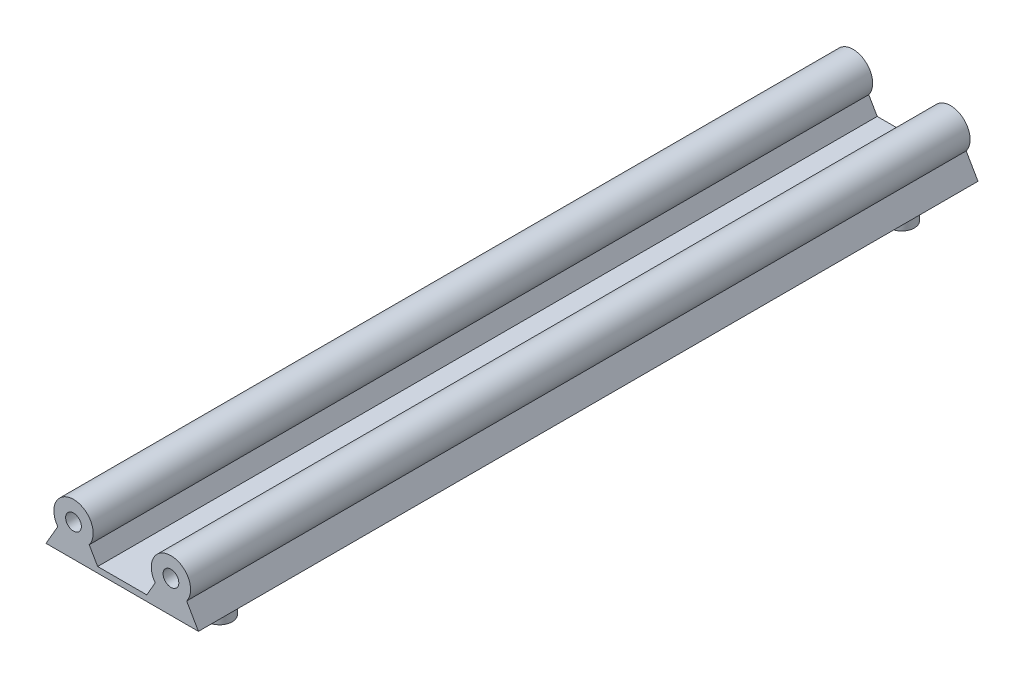
SolidWorks part; units mm, degrees
ref_plane "Front Plane" through (0, 0, 0) normal (0, 0, 1) x (1, 0, 0)
ref_plane "Top Plane" through (0, 0, 0) normal (0, 1, 0) x (1, 0, 0)
ref_plane "Right Plane" through (0, 0, 0) normal (1, 0, 0) x (0, 0, -1)
sketch "Sketch1" plane through (0, 0, 0) normal (0, 0, 1) x (1, 0, 0)
  line L0 (-4, -3) -> (4, -3) construction
  line L1 (-4, -3) -> (-7, -8.1962)
  line L2 (4, -3) -> (7, -8.1962)
  line L3 (-7, -8.1962) -> (7, -8.1962)
  line L4 (28.8, -3) -> (31.8, -8.1962)
  line L5 (17.8, -8.1962) -> (31.8, -8.1962)
  line L6 (20.8, -3) -> (17.8, -8.1962)
  circle A0 centre (0, 0) radius 5
  arc A1 (-4, -3) -> (4, -3) centre (0, 0) cw
  arc A2 (20.8, -3) -> (28.8, -3) centre (24.8, 0) cw
  dimension "D1" = 3
  dimension "D2" = 2
  dimension "D3" = 8
extrude "Boss-Extrude1" add sketch "Sketch1" along normal blind 220 contours A0 L0 | L0 A0 | A0 L1 L3 L2 | L4 L5 L6 A2
sketch "Sketch3" plane through (0, 0, 220) normal (0, 0, 1) x (1, 0, 0)
  line L0 (7, -8.1962) -> (17.8, -8.1962)
  line L1 (6.15, -6.7239) -> (18.65, -6.7239)
  line L2 (4, -3) -> (7, -8.1962) construction
  line L3 (20.8, -3) -> (17.8, -8.1962) construction
  line L4 (18.65, -6.7239) -> (18.65, -8.1962)
  line L5 (17.8, -8.1962) -> (31.8, -8.1962) construction
  line L6 (18.65, -8.1962) -> (17.8, -8.1962)
  line L7 (6.15, -6.7239) -> (6.15, -8.1962)
  line L8 (-7, -8.1962) -> (7, -8.1962) construction
  line L9 (6.15, -8.1962) -> (7, -8.1962)
  dimension "D1" = 12.5
sketch "Sketch4" plane through (0, -8.1962, 0) normal (0, -1, 0) x (1, 0, 0)
  line L0 (24.8, 220) -> (24.8, 0) construction
  line L1 (17.8, 220) -> (31.8, 220) construction
  line L2 (17.8, 0) -> (31.8, 0) construction
  line L3 (0, 0) -> (0, 220) construction
  line L4 (-7, 220) -> (7, 220) construction
  circle A0 centre (0, 196.8) radius 3.2
  circle A1 centre (24.8, 196.8) radius 3.2
  circle A2 centre (24.8, 172) radius 3.2
  circle A3 centre (24.8, 147.2) radius 3.2
  circle A4 centre (24.8, 122.4) radius 3.2
  circle A5 centre (24.8, 97.6) radius 3.2
  circle A6 centre (24.8, 72.8) radius 3.2
  circle A7 centre (24.8, 48) radius 3.2
  circle A8 centre (24.8, 23.2) radius 3.2
  circle A9 centre (0, 172) radius 3.2
  circle A10 centre (0, 147.2) radius 3.2
  circle A11 centre (0, 122.4) radius 3.2
  circle A12 centre (0, 97.6) radius 3.2
  circle A13 centre (0, 72.8) radius 3.2
  circle A14 centre (0, 48) radius 3.2
  circle A15 centre (0, 23.2) radius 3.2
  dimension "D1" = 2
  dimension "D3" = 23.2
  dimension "D2" = 8
extrude "Boss-Extrude3" add sketch "Sketch4" along normal blind 6
extrude "Boss-Extrude4" add sketch "Sketch3" against normal blind 220
sketch "Sketch5" plane through (0, 0, 0) normal (0, 0, -1) x (-1, 0, 0)
  circle A0 centre (0, 0) radius 1.37
  circle A1 centre (-24.8, 0) radius 1.37
  dimension "D1" = 2
extrude "Cut-Extrude1" cut sketch "Sketch5" against normal blind 7
sketch "Sketch6" plane through (0, 0, 220) normal (0, 0, 1) x (1, 0, 0)
  circle A0 centre (0, 0) radius 1.37
  circle A1 centre (24.8, 0) radius 1.37
  dimension "D1" = 2
extrude "Cut-Extrude2" cut sketch "Sketch6" against normal blind 7
sketch "Sketch7" plane through (0, -14.1962, 0) normal (0, -1, 0) x (1, 0, 0)
  circle A0 centre (0, 172) radius 3.2
  circle A1 centre (24.8, 172) radius 3.2
  circle A2 centre (24.8, 147.2) radius 3.2
  circle A3 centre (24.8, 122.4) radius 3.2
  circle A4 centre (24.8, 97.6) radius 3.2
  circle A5 centre (24.8, 72.8) radius 3.2
  circle A6 centre (24.8, 48) radius 3.2
  circle A7 centre (0, 147.2) radius 3.2
  circle A8 centre (0, 122.4) radius 3.2
  circle A9 centre (0, 97.6) radius 3.2
  circle A10 centre (0, 72.8) radius 3.2
  circle A11 centre (0, 48) radius 3.2
  dimension "D1" = 2
  dimension "D2" = 6
extrude "Cut-Extrude3" cut sketch "Sketch7" against normal blind 6
sketch "Sketch9" plane through (0, 0, 0) normal (0, 0, -1) x (-1, 0, 0)
  line L6 (-28.8, -3) -> (-31.8, -8.1962)
  line L7 (-31.8, -8.1962) -> (7, -8.1962)
  line L8 (7, -8.1962) -> (4, -3)
  line L9 (-4, -3) -> (-6.15, -6.7239)
  line L10 (-6.15, -6.7239) -> (-18.65, -6.7239)
  line L11 (-18.65, -6.7239) -> (-20.8, -3)
  line L12 (-28.8, -3) -> (-31.8, -8.1962)
  line L13 (-31.8, -8.1962) -> (7, -8.1962)
  line L14 (7, -8.1962) -> (4, -3)
  line L15 (-4, -3) -> (-6.15, -6.7239)
  line L16 (-6.15, -6.7239) -> (-18.65, -6.7239)
  line L17 (-18.65, -6.7239) -> (-20.8, -3)
  arc A2 (4, -3) -> (-4, -3) centre (0, 0) ccw
  arc A3 (-20.8, -3) -> (-28.8, -3) centre (-24.8, 0) ccw
  arc A4 (4, -3) -> (-4, -3) centre (0, 0) ccw
  arc A5 (-20.8, -3) -> (-28.8, -3) centre (-24.8, 0) ccw
  dimension "D1" = 0
extrude "Cut-Extrude4" cut sketch "Sketch9" against normal blind 10.8
sketch "Sketch10" plane through (0, 0, 220) normal (0, 0, 1) x (1, 0, 0)
  line L6 (20.8, -3) -> (18.65, -6.7239)
  line L7 (18.65, -6.7239) -> (6.15, -6.7239)
  line L8 (6.15, -6.7239) -> (4, -3)
  line L9 (-4, -3) -> (-7, -8.1962)
  line L10 (-7, -8.1962) -> (31.8, -8.1962)
  line L11 (31.8, -8.1962) -> (28.8, -3)
  line L12 (20.8, -3) -> (18.65, -6.7239)
  line L13 (18.65, -6.7239) -> (6.15, -6.7239)
  line L14 (6.15, -6.7239) -> (4, -3)
  line L15 (-4, -3) -> (-7, -8.1962)
  line L16 (-7, -8.1962) -> (31.8, -8.1962)
  line L17 (31.8, -8.1962) -> (28.8, -3)
  arc A2 (4, -3) -> (-4, -3) centre (0, 0) ccw
  arc A3 (28.8, -3) -> (20.8, -3) centre (24.8, 0) ccw
  arc A4 (4, -3) -> (-4, -3) centre (0, 0) ccw
  arc A5 (28.8, -3) -> (20.8, -3) centre (24.8, 0) ccw
  dimension "D1" = 0
extrude "Cut-Extrude5" cut sketch "Sketch10" against normal blind 10.8
sketch "Sketch11" plane through (0, 0, 209.2) normal (0, 0, 1) x (1, 0, 0)
  circle A0 centre (0, 0) radius 2
  circle A1 centre (24.8, 0) radius 2
  dimension "D1" = 2
extrude "Cut-Extrude6" cut sketch "Sketch11" against normal blind 7
sketch "Sketch12" plane through (0, 0, 10.8) normal (0, 0, -1) x (-1, 0, 0)
  circle A0 centre (0, 0) radius 2
  circle A1 centre (-24.8, 0) radius 2
  dimension "D1" = 2
extrude "Cut-Extrude7" cut sketch "Sketch12" against normal blind 7
